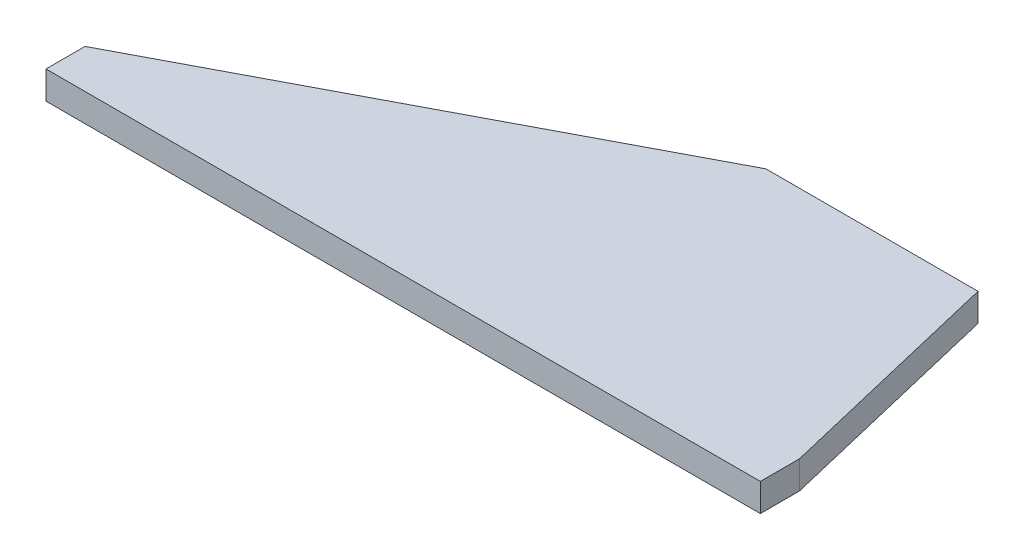
SolidWorks part; units mm, degrees
ref_plane "Front Plane" through (0, 0, 0) normal (0, 0, 1) x (1, 0, 0)
ref_plane "Top Plane" through (0, 0, 0) normal (0, 1, 0) x (1, 0, 0)
ref_plane "Right Plane" through (0, 0, 0) normal (1, 0, 0) x (0, 0, -1)
sketch "Sketch1" plane through (0, 0, 0) normal (0, 1, 0) x (1, 0, 0)
  line L0 (0, 0) -> (101.6, 53.34)
  line L1 (0, -8.89) -> (162.56, -8.89)
  line L2 (0, -8.89) -> (0, 0)
  line L4 (162.56, -8.89) -> (162.56, 0)
  line L5 (101.6, 53.34) -> (149.86, 53.34)
  line L6 (149.86, 53.34) -> (162.56, 0)
  dimension "D1" = 162.56
  dimension "D2" = 101.6
  dimension "D3" = 53.34
  dimension "D4" = 149.86
  dimension "D5" = 8.89
extrude "Boss-Extrude1" add sketch "Sketch1" along normal blind 6.35
ref_plane "midplane" through (0, 3.175, 0) normal (0, 1, 0) x (1, 0, 0)
ref_plane "back plane" through (165.1, 0, 0) normal (1, 0, 0) x (0, 0, -1)
